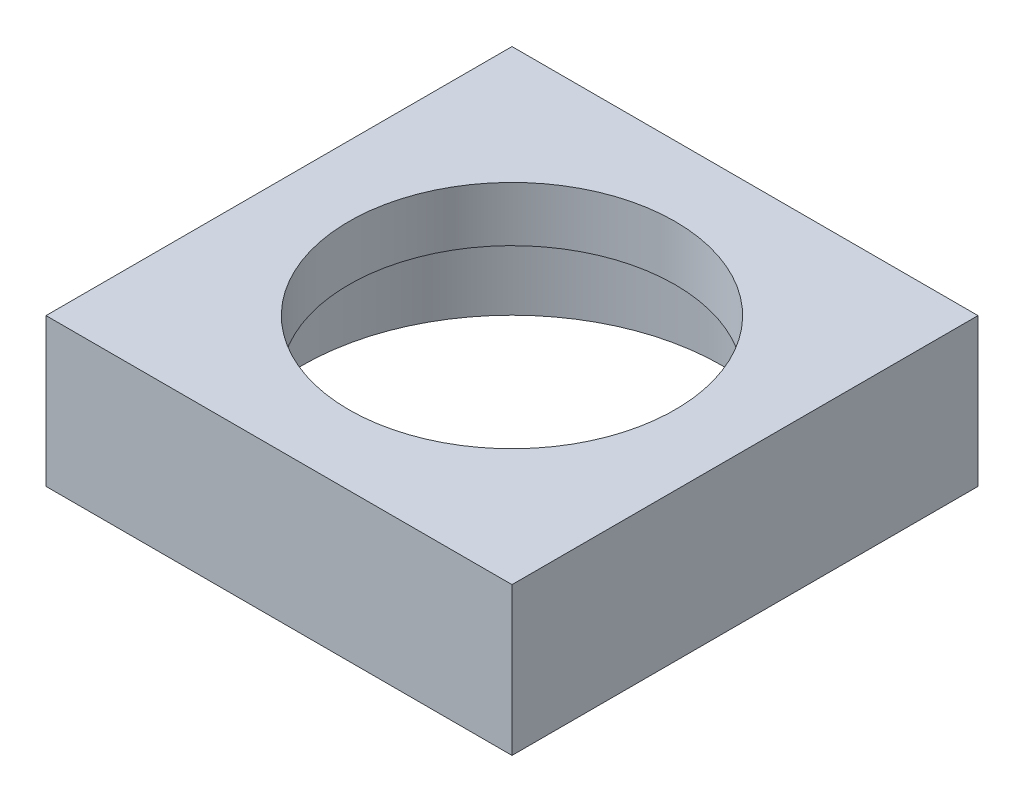
SolidWorks part; units mm, degrees
ref_plane "Front Plane" through (0, 0, 0) normal (0, 0, 1) x (1, 0, 0)
ref_plane "Top Plane" through (0, 0, 0) normal (0, 1, 0) x (1, 0, 0)
ref_plane "Right Plane" through (0, 0, 0) normal (1, 0, 0) x (0, 0, -1)
sketch "Sketch1" plane through (0, 0, 0) normal (0, 1, 0) x (1, 0, 0)
  line L1 (0, 0) -> (10, 0)
  line L2 (0, 0) -> (0, -10)
  line L3 (0, -10) -> (10, -10)
  line L4 (10, 0) -> (10, -10)
  circle A0 centre (5, -5) radius 4.5
  point P8 (5, 0)
  point P10 (0, -5)
  dimension "D3" = 9
  dimension "D1" = 10
  dimension "D2" = 10
extrude "Boss-Extrude1" add sketch "Sketch1" along normal blind 3.175
sketch "Sketch2" plane through (0, 3.175, 0) normal (0, 1, 0) x (1, 0, 0)
  line L1 (0, 0) -> (10, 0)
  line L2 (0, 0) -> (0, -10)
  line L3 (0, -10) -> (10, -10)
  line L4 (10, 0) -> (10, -10)
  circle A0 centre (5, -5) radius 3.5
  circle A1 centre (5, -5) radius 4.5 construction
  point P8 (0, 0)
  dimension "D1" = 7
extrude "Boss-Extrude2" add sketch "Sketch2" against normal blind 1.175
